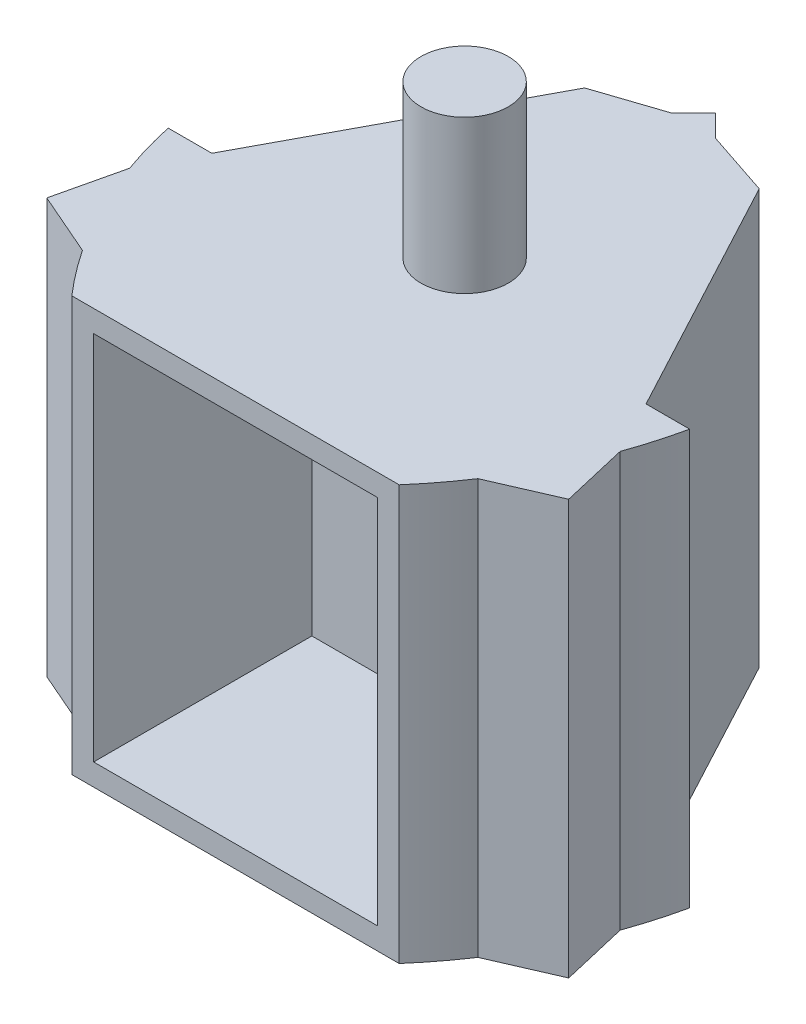
SolidWorks part; units mm, degrees
ref_plane "Front Plane" through (0, 0, 0) normal (0, 0, 1) x (1, 0, 0)
ref_plane "Top Plane" through (0, 0, 0) normal (0, 1, 0) x (1, 0, 0)
ref_plane "Right Plane" through (0, 0, 0) normal (1, 0, 0) x (0, 0, -1)
sketch "Sketch1" plane through (0, 0, 0) normal (0, 1, 0) x (1, 0, 0)
  line L0 (-4, 0) -> (4, 0)
  line L1 (-7.5, -20) -> (-4, 0)
  line L2 (-7.5, -20) -> (7.5, -20)
  line L3 (4, 0) -> (7.5, -20)
  line L4 (-2, 0) -> (0, 1)
  line L5 (0, 1) -> (2, 0)
  line L6 (2, 0) -> (-2, 0)
  line L7 (-5.9486, -11.1347) -> (-10.9486, -11.1347)
  line L8 (5.9486, -11.1347) -> (10.9486, -11.1347)
  line L9 (-10.9486, -11.1347) -> (-7.5, -20)
  line L10 (-5.9486, -11.1347) -> (-7.5, -20)
  line L11 (10.9486, -11.1347) -> (7.5, -20)
  line L12 (7.5, -20) -> (5.9486, -11.1347)
  line L13 (-9.2243, -15.5674) -> (-11.0882, -16.2924)
  line L14 (-11.0882, -16.2924) -> (-8.4992, -17.4313)
  line L15 (-8.4992, -17.4313) -> (-9.9494, -13.7034)
  line L16 (-9.9494, -13.7034) -> (-11.0882, -16.2924)
  line L17 (9.2243, -15.5674) -> (11.0882, -16.2924)
  line L18 (9.9494, -13.7034) -> (11.0882, -16.2924)
  line L19 (11.0882, -16.2924) -> (8.4992, -17.4313)
  line L20 (8.4992, -17.4313) -> (9.9494, -13.7034)
  point P0 (2, 0)
  point P3 (0, 0)
  point P4 (0, 1)
  point P6 (-2, 0)
  point P10 (0, -20)
  point P12 (5.9486, -11.1347)
  point P14 (-5.9486, -11.1347)
  point P19 (-9.9494, -13.7034)
  point P20 (-9.2243, -15.5674)
  point P21 (-8.4992, -17.4313)
  point P24 (9.9494, -13.7034)
  point P27 (8.4992, -17.4313)
  dimension "D1" = 8
  dimension "D2" = 2
  dimension "D3" = 15
  dimension "D4" = 2
  dimension "D5" = 1
  dimension "D6" = 9
  dimension "D7" = 5
  dimension "D8" = 5
  dimension "D9" = 2
  dimension "D10" = 2
  dimension "D11" = 2
  dimension "D12" = 2
extrude "Boss-Extrude1" add sketch "Sketch1" along normal blind 19 contours L3 L0 L1 L2 | L7 L9 L1 | L9 L16 L13 | L13 L14 L9 | L11 L8 L3 | L18 L11 L17 | L19 L17 L11 | L5 L4 L0
sketch "Sketch2" plane through (0, 19, 0) normal (0, 1, 0) x (1, 0, 0)
  line L0 (0, 1) -> (0, -20)
  line L1 (-7.5, -20) -> (7.5, -20) construction
  circle A0 centre (0, -9.5) radius 2
extrude "Boss-Extrude2" add sketch "Sketch2" along normal blind 7 contours L0 A0 | L0 A0
sketch "Sketch3" plane through (0, 0, 0) normal (0, -1, 0) x (1, 0, 0)
  line L0 (0, -1) -> (0, 20)
  line L1 (-7.5, 20) -> (7.5, 20) construction
  circle A0 centre (0, 9.5) radius 2
extrude "Boss-Extrude3" add sketch "Sketch3" along normal blind 7 contours L0 A0 | L0 A0
sketch "Sketch4" plane through (0, 0, 0) normal (0, -1, 0) x (1, 0, 0)
  line L0 (-5.9486, 11.1347) -> (-10.9486, 11.1347) construction
  line L1 (5.9486, 11.1347) -> (10.9486, 11.1347) construction
  line L2 (9.9486, 11.1347) -> (4, 0)
  line L3 (4, 0) -> (5.9486, 11.1347)
  line L4 (5.9486, 11.1347) -> (9.9486, 11.1347)
  line L5 (-5.9486, 11.1347) -> (-9.9486, 11.1347)
  line L6 (-9.9486, 11.1347) -> (-4, 0)
  line L7 (-4, 0) -> (-5.9486, 11.1347)
  point P0 (-9.9486, 11.1347)
  point P1 (9.9486, 11.1347)
  dimension "D1" = 4
  dimension "D2" = 4
extrude "Boss-Extrude4" add sketch "Sketch4" against normal blind 19
sketch "Sketch5" plane through (0, 0, 0) normal (0, -1, 0) x (1, 0, 0)
  line L0 (9.9494, 13.7034) -> (8.4992, 17.4313)
  line L1 (8.4992, 17.4313) -> (11.0882, 16.2924)
  line L2 (11.0882, 16.2924) -> (9.9494, 13.7034)
extrude "Cut-Extrude1" cut sketch "Sketch5" against normal blind 19
sketch "Sketch6" plane through (0, 0, 0) normal (0, -1, 0) x (1, 0, 0)
  line L0 (-9.9494, 13.7034) -> (-8.4992, 17.4313)
  line L1 (-8.4992, 17.4313) -> (-11.0882, 16.2924)
  line L2 (-11.0882, 16.2924) -> (-9.9494, 13.7034)
extrude "Cut-Extrude2" cut sketch "Sketch6" against normal blind 19
sketch "Sketch7" plane through (0, 0, 0) normal (0, -1, 0) x (1, 0, 0)
  line L0 (10.9486, 11.1347) -> (11.9486, 11.1347)
  line L1 (11.9486, 11.1347) -> (7.5, 20)
  line L2 (7.5, 20) -> (10.9486, 11.1347)
  line L3 (-11.9486, 11.1347) -> (-7.5, 20)
  line L4 (-7.5, 20) -> (-10.9486, 11.1347)
  line L5 (-10.9486, 11.1347) -> (-11.9486, 11.1347)
  point P0 (-11.9486, 11.1347)
  point P1 (11.9486, 11.1347)
  dimension "D1" = 2
  dimension "D2" = 2
extrude "Boss-Extrude5" add sketch "Sketch7" against normal blind 19
sketch "Sketch8" plane through (0, 0, 0) normal (0, -1, 0) x (1, 0, 0)
  line L0 (2, 0) -> (0, -2)
  line L1 (0, -2) -> (-2, 0)
  line L2 (-2, 0) -> (0, -1)
  line L3 (0, -1) -> (2, 0)
  point P0 (0, -2)
  dimension "D1" = 1
extrude "Boss-Extrude6" add sketch "Sketch8" against normal blind 19
sketch "Sketch9" plane through (0, 0, 0) normal (0, -1, 0) x (1, 0, 0)
  line L0 (0, -2) -> (2, 0) construction
  line L1 (-2, 0) -> (0, -2) construction
  line L2 (-1, -1) -> (-4, 0)
  line L3 (-4, 0) -> (-2, 0)
  line L4 (-2, 0) -> (-1, -1)
  line L5 (1, -1) -> (4, 0)
  line L6 (4, 0) -> (2, 0)
  line L7 (2, 0) -> (1, -1)
  point P0 (1, -1)
  point P1 (-1, -1)
extrude "Boss-Extrude7" add sketch "Sketch9" against normal blind 19
sketch "Sketch10" plane through (0, 0, 0) normal (0, -1, 0) x (1, 0, 0)
  line L0 (-7.5, 20) -> (-11.9486, 11.1347) construction
  line L1 (11.9486, 11.1347) -> (7.5, 20) construction
  line L2 (11.0698, 12.886) -> (11.9587, 16.6886)
  line L3 (11.9587, 16.6886) -> (8.3788, 18.2487)
  line L4 (8.3788, 18.2487) -> (11.0698, 12.886)
  line L5 (-8.3788, 18.2487) -> (-11.0698, 12.886)
  line L6 (-11.0698, 12.886) -> (-11.9587, 16.6886)
  line L7 (-11.9587, 16.6886) -> (-8.3788, 18.2487)
  point P0 (-11.9587, 16.6886)
  point P3 (-9.7243, 15.5674)
  point P4 (9.7243, 15.5674)
  point P5 (11.9587, 16.6886)
  point P8 (11.0698, 12.886)
  point P9 (8.3788, 18.2487)
  point P10 (-11.0698, 12.886)
  point P11 (-8.3788, 18.2487)
  dimension "D1" = 2.5
  dimension "D2" = 3
  dimension "D3" = 3
extrude "Boss-Extrude8" add sketch "Sketch10" against normal blind 19
sketch "Sketch13" plane through (0, 0, 0) normal (0, -1, 0) x (1, 0, 0)
  line L0 (11.9486, 11.1347) -> (7.5, 20)
  line L1 (11.0698, 12.886) -> (11.9587, 16.6886)
  line L2 (11.9587, 16.6886) -> (8.3788, 18.2487)
  line L3 (-11.9486, 11.1347) -> (-7.5, 20)
  line L4 (-8.3788, 18.2487) -> (-11.9587, 16.6886)
  line L5 (-11.9587, 16.6886) -> (-11.0698, 12.886)
  arc A0 (11.9486, 11.1347) -> (7.5, 20) centre (-7.5931, 6.8775) ccw
  arc A1 (-11.9486, 11.1347) -> (-7.5, 20) centre (7.5931, 6.8775) cw
  point P3 (11.0698, 12.886)
  line M6 (11.9486, 11.1347) -> (11.0698, 12.886)
  line M7 (11.0698, 12.886) -> (11.9587, 16.6886)
  line M9 (8.3788, 18.2487) -> (7.5, 20)
  line M11 (-7.5, 20) -> (-8.3788, 18.2487)
  line M12 (-8.3788, 18.2487) -> (-11.9587, 16.6886)
  line M14 (-11.0698, 12.886) -> (-11.9486, 11.1347)
extrude "Boss-Extrude9" add sketch "Sketch13" against normal blind 19 contours A0 M6 M7 | L2 A0 M9 | A1 M12 M11 | A1 L5 M14
sketch "Sketch14" plane through (0, 0, 20) normal (0, 0, 1) x (1, 0, 0)
  line L0 (-7.5, 19) -> (7.5, 19) construction
  line L1 (-7.5, 0) -> (7.5, 0) construction
  line L3 (-6.5, 18) -> (6.5, 18)
  line L4 (-6.5, 18) -> (-6.5, 1)
  line L5 (-6.5, 1) -> (6.5, 1)
  line L6 (6.5, 18) -> (6.5, 1)
  point P0 (-6.5, 19)
  point P1 (-6.5, 18)
  point P5 (6.5, 0)
  point P6 (6.5, 1)
  dimension "D1" = 1
  dimension "D2" = 1
  dimension "D3" = 1
  dimension "D4" = 1
extrude "Cut-Extrude3" cut sketch "Sketch14" against normal blind 10
